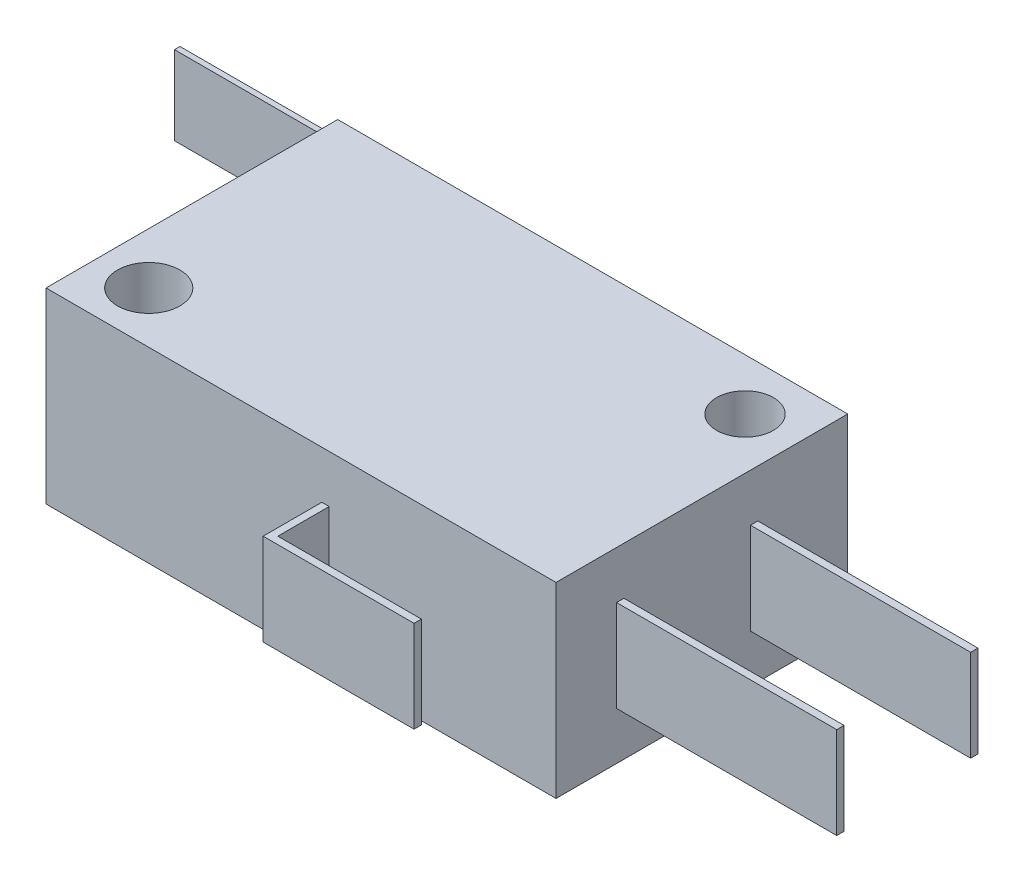
SolidWorks part; units mm, degrees
ref_plane "Front Plane" through (0, 0, 0) normal (0, 0, 1) x (1, 0, 0)
ref_plane "Top Plane" through (0, 0, 0) normal (0, 1, 0) x (1, 0, 0)
ref_plane "Right Plane" through (0, 0, 0) normal (1, 0, 0) x (0, 0, -1)
sketch "Sketch1" plane through (0, 0, 0) normal (0, 1, 0) x (1, 0, 0)
  line L1 (-13.9, -7.95) -> (13.9, -7.95)
  line L2 (-13.9, -7.95) -> (-13.9, 7.95)
  line L3 (-13.9, 7.95) -> (13.9, 7.95)
  line L4 (13.9, -7.95) -> (13.9, 7.95)
  line L5 (0, 7.95) -> (0, -7.95) construction
  line L6 (-13.9, 0) -> (13.9, 0) construction
  point P0 (0, 0)
  dimension "D1" = 27.8
  dimension "D2" = 15.9
extrude "Boss-Extrude1" add sketch "Sketch1" along normal mid plane 10.2
sketch "Sketch2" plane through (0, 0, 0) normal (0, 1, 0) x (1, 0, 0)
  line L0 (13.9, 7.95) -> (-13.9, 7.95) construction
  line L5 (11.1, 5.15) -> (-11.1, 5.15)
  line L6 (11.1, 5.15) -> (11.1, -5.15)
  line L7 (11.1, -5.15) -> (-11.1, -5.15)
  line L8 (-11.1, 5.15) -> (-11.1, -5.15)
  line L9 (0, -5.15) -> (0, 5.15) construction
  line L10 (11.1, 0) -> (-11.1, 0) construction
  line L11 (13.9, -7.95) -> (13.9, 7.95) construction
  circle A0 centre (11.1, 5.15) radius 1.55
  circle A1 centre (-11.1, -5.15) radius 1.7
  point P0 (0, 0)
  point P65 (0, 0)
  dimension "D1" = 3.1
  dimension "D5" = 3.4
  dimension "D2" = 10.3
  dimension "D3" = 22.2
  dimension "D4" = 2.8
  dimension "D6" = 2.8
extrude "Cut-Extrude1" cut sketch "Sketch2" against normal through all both and the other way through all contours A1 | A0
sketch "Sketch3" plane through (0, 0, 0) normal (0, 1, 0) x (1, 0, 0)
  line L0 (2.9, 7.95) -> (2.9, 10.05)
  line L1 (13.9, 7.95) -> (-13.9, 7.95) construction
  line L2 (2.9, 10.05) -> (-24.6, 10.05)
  line L3 (-24.6, 10.05) -> (-24.6, 9.75)
  line L4 (-24.6, 9.75) -> (2.6, 9.75)
  line L5 (2.6, 9.75) -> (2.6, 7.95)
  line L6 (2.6, 7.95) -> (2.9, 7.95)
  circle A0 centre (11.1, 5.15) radius 1.55 construction
  circle A1 centre (-11.1, -5.15) radius 1.7 construction
  dimension "D1" = 8.2
  dimension "D2" = 0.3
  dimension "D3" = 0.3
  dimension "D4" = 35.7
  dimension "D5" = 15.2
extrude "Boss-Extrude2" add sketch "Sketch3" along normal mid plane 4.3
sketch "Sketch4" plane through (0, 0, 0) normal (0, 1, 0) x (1, 0, 0)
  line L0 (13.9, 7.95) -> (-13.9, 7.95) construction
  circle A0 centre (-8.8992, 7.95) radius 1.8
extrude "Boss-Extrude6" add sketch "Sketch4" along normal mid plane 4.3 separate body contours A0
sketch "Sketch5" plane through (0, 0, 0) normal (0, 1, 0) x (1, 0, 0)
  line L0 (13.9, 3.05) -> (25.9, 3.05)
  line L1 (13.9, -7.95) -> (13.9, 7.95) construction
  line L2 (25.9, 3.05) -> (25.9, 2.65)
  line L3 (25.9, 2.65) -> (13.9, 2.65)
  line L4 (13.9, 2.65) -> (13.9, 3.05)
  line L5 (-13.9, 7.95) -> (-13.9, -7.95) construction
  line L6 (13.9, 7.95) -> (-13.9, 7.95) construction
  dimension "D1" = 0.4
  dimension "D2" = 39.8
  dimension "D3" = 4.9
extrude "Boss-Extrude7" add sketch "Sketch5" along normal mid plane 5
pattern_linear "LPattern1" count 2 spacing 7.3 along (0, 0, 1) of "Boss-Extrude7"
sketch "Sketch6" plane through (0, 0, 0) normal (0, 1, 0) x (1, 0, 0)
  line L0 (1.5355, -7.95) -> (1.5355, -10.75)
  line L1 (-13.9, -7.95) -> (13.9, -7.95) construction
  line L2 (1.5355, -10.75) -> (9.361, -10.75)
  line L3 (9.361, -10.75) -> (9.361, -11.15)
  line L4 (9.361, -11.15) -> (1.1355, -11.15)
  line L5 (1.1355, -11.15) -> (1.1355, -7.95)
  line L6 (1.1355, -7.95) -> (1.5355, -7.95)
  dimension "D1" = 3.2
  dimension "D2" = 0.4
  dimension "D3" = 0.4
extrude "Boss-Extrude8" add sketch "Sketch6" along normal mid plane 5
equation "\"0。3\"=0.835671"
